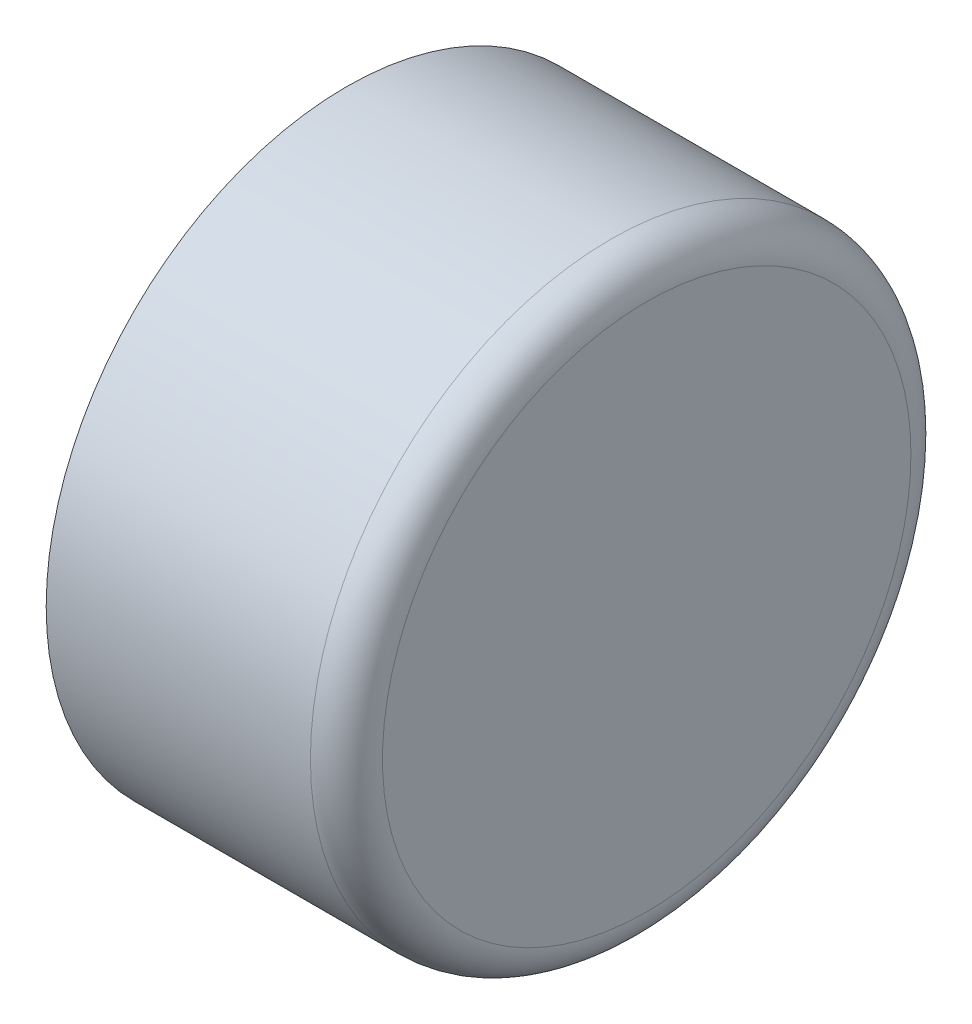
SolidWorks part; units mm, degrees
ref_plane "Front Plane" through (0, 0, 0) normal (0, 0, 1) x (1, 0, 0)
ref_plane "Top Plane" through (0, 0, 0) normal (0, 1, 0) x (1, 0, 0)
ref_plane "Right Plane" through (0, 0, 0) normal (1, 0, 0) x (0, 0, -1)
sketch "Sketch2" plane through (0, 0, 0) normal (0, 1, 0) x (1, 0, 0)
  line L0 (0, 0) -> (0, 8.001)
  line L1 (-1.524, 9.525) -> (-7.9248, 9.525)
  line L2 (-7.9248, 9.525) -> (-7.9248, 11.1125)
  line L3 (-7.9248, 11.1125) -> (-9.525, 11.1125)
  line L4 (-9.525, 11.1125) -> (-9.525, 12.7)
  line L5 (-9.525, 12.7) -> (1.651, 12.7)
  line L6 (3.175, 11.176) -> (3.175, 0)
  line L7 (3.175, 0) -> (0, 0)
  arc A0 (1.651, 12.7) -> (3.175, 11.176) centre (1.651, 11.176) cw
  arc A1 (0, 8.001) -> (-1.524, 9.525) centre (-1.524, 8.001) ccw
  dimension "D8" = 1.524
  dimension "D1" = 1.6002
  dimension "D2" = 12.7
  dimension "D3" = 11.1125
  dimension "D4" = 9.525
  dimension "D5" = 12.7
  dimension "D6" = 3.175
  dimension "D7" = 3.175
revolve "Revolve1" add sketch "Sketch2" angle 360 about L7
